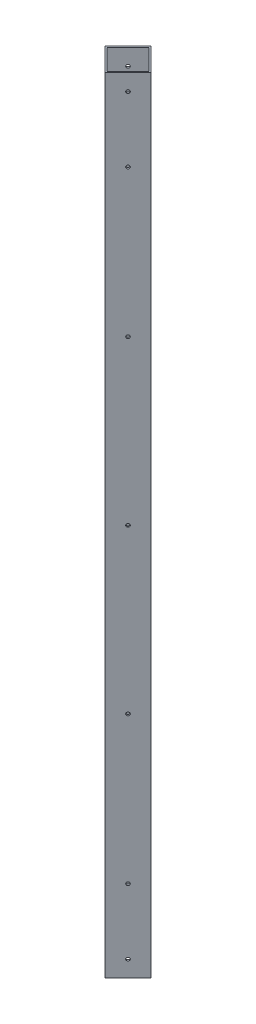
SolidWorks part; units mm, degrees
material "1060 合金"
ref_plane "前视基准面" through (0, 0, 0) normal (0, 0, 1) x (1, 0, 0)
ref_plane "上视基准面" through (0, 0, 0) normal (0, 1, 0) x (1, 0, 0)
ref_plane "右视基准面" through (0, 0, 0) normal (1, 0, 0) x (0, 0, -1)
other "Configuration Table"
sketch "草图1" plane through (0, 0, 0) normal (0, 1, 0) x (1, 0, 0)
  line L1 (14.1421, 0) -> (0, 14.1421)
  line L2 (0, 14.1421) -> (-14.1421, 0)
  line L3 (-14.1421, 0) -> (0, -14.1421)
  line L4 (0, -14.1421) -> (14.1421, 0)
  line L5 (12.7279, 0) -> (0, 12.7279)
  line L6 (0, 12.7279) -> (-12.7279, 0)
  line L7 (-12.7279, 0) -> (0, -12.7279)
  line L8 (0, -12.7279) -> (12.7279, 0)
  circle A0 centre (0, 0) radius 10 construction
  circle A1 centre (0, 0) radius 9 construction
  dimension "D1" = 20
  dimension "D2" = 18
extrude "凸台-拉伸1" add sketch "草图1" along normal mid plane 480
sketch "草图3" plane through (7.0711, 0, 7.0711) normal (0.7071, 0, 0.7071) x (0.7071, 0, -0.7071)
  line L0 (-10, 240) -> (10, 240) construction
  line L1 (-96.682, 0) -> (144.7645, 0) construction
  circle A0 centre (0, 230) radius 1
  circle A1 centre (0, 190) radius 1
  circle A2 centre (0, -190) radius 1
  circle A3 centre (0, -230) radius 1
  dimension "D1" = 2
  dimension "D3" = 2
  dimension "D4" = 40
  dimension "D2" = 10
extrude "切除-拉伸1" cut sketch "草图3" against normal through all
sketch "草图4" plane through (7.0711, 0, 7.0711) normal (0.7071, 0, 0.7071) x (0.7071, 0, -0.7071)
  circle A0 centre (0, 100) radius 1
  circle A1 centre (0, 0) radius 1
  circle A2 centre (0, -100) radius 1
  dimension "D1" = 2
  dimension "D2" = 2
  dimension "D3" = 2
  dimension "D4" = 100
  dimension "D5" = 100
extrude "切除-拉伸2" cut sketch "草图4" against normal through all
